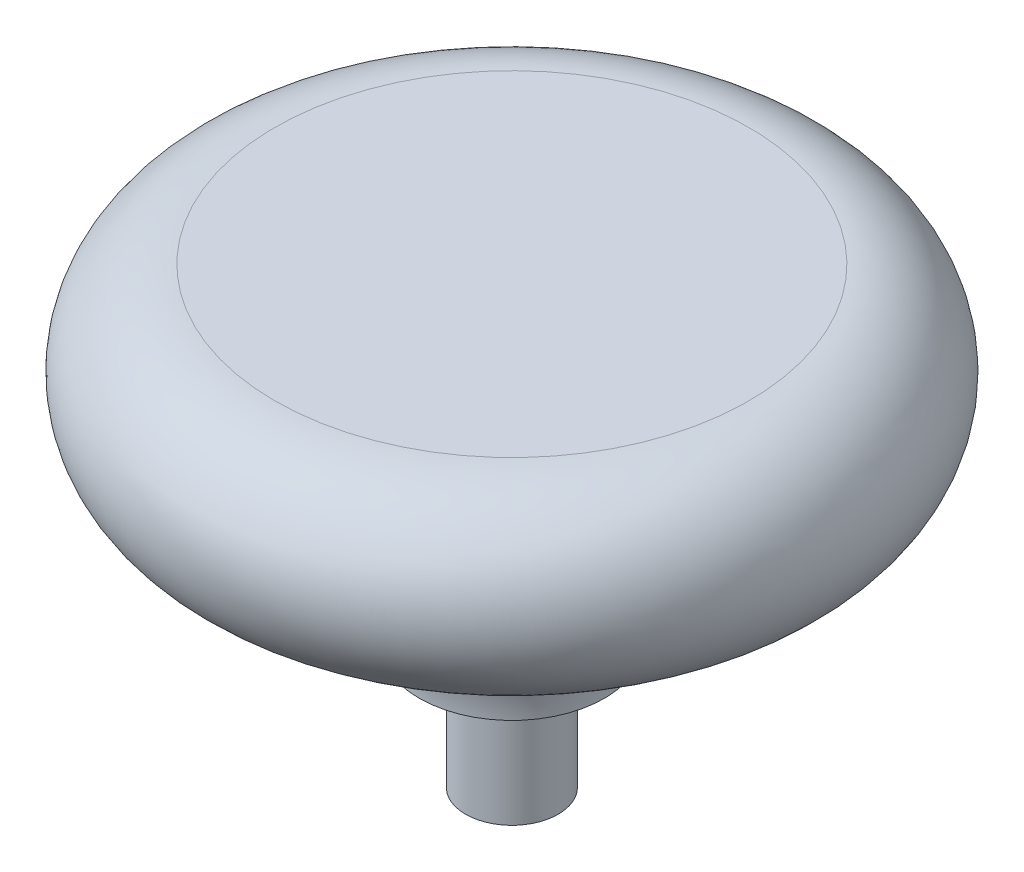
SolidWorks part; units mm, degrees
ref_plane "Front Plane" through (0, 0, 0) normal (0, 0, 1) x (1, 0, 0)
ref_plane "Top Plane" through (0, 0, 0) normal (0, 1, 0) x (1, 0, 0)
ref_plane "Right Plane" through (0, 0, 0) normal (1, 0, 0) x (0, 0, -1)
sketch "Sketch1" plane through (0, 0, 0) normal (0, 0, 1) x (1, 0, 0)
  line L0 (0, 28.9172) -> (0, -28.9172) construction
  line L1 (0, 0) -> (2.25, 0)
  line L2 (2.25, 0) -> (2.25, 6)
  line L3 (2.25, 6) -> (4.5, 6)
  line L4 (0, 22) -> (11.5, 22)
  line L5 (16, 30.3659) -> (16, 3.1759) construction
  line L6 (0, 0) -> (0, 22)
  arc A0 (11.5, 13) -> (4.5, 6) centre (11.5, 6) ccw
  arc A1 (11.5, 13) -> (11.5, 22) centre (11.5, 17.5) ccw
  point P4 (0, 0)
  dimension "D1" = 7
  dimension "D5" = 4.5
  dimension "D2" = 2.25
  dimension "D3" = 6
  dimension "D4" = 22
  dimension "D6" = 16
revolve "Revolve1" add sketch "Sketch1" angle 360 about L0
